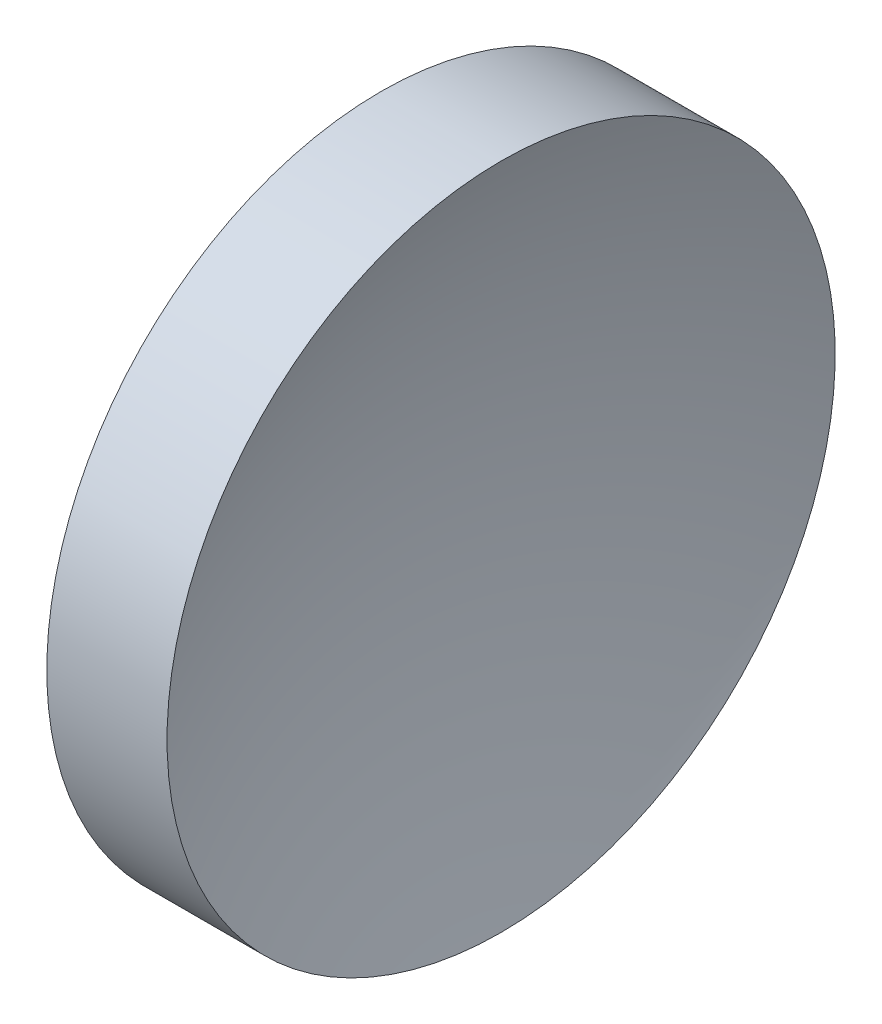
SolidWorks part; units mm, degrees
ref_plane "前视基准面" through (0, 0, 0) normal (0, 0, 1) x (1, 0, 0)
ref_plane "上视基准面" through (0, 0, 0) normal (0, 1, 0) x (1, 0, 0)
ref_plane "右视基准面" through (0, 0, 0) normal (1, 0, 0) x (0, 0, -1)
sketch "草图1" plane through (0, 0, 0) normal (0, 0, 1) x (1, 0, 0)
  line L0 (55.0074, 32.5787) -> (69.3049, 32.5787) construction
  line L1 (57.3582, 32.5787) -> (57.3582, 45.0787)
  line L2 (59.3582, 32.5787) -> (57.3582, 32.5787)
  line L3 (57.3582, 45.0787) -> (61.8582, 45.0787)
  arc A0 (61.8582, 45.0787) -> (59.3582, 32.5787) centre (91.8582, 32.5787) ccw
  dimension "D3" = 32.5
  dimension "D1" = 4.5
  dimension "D2" = 12.5
revolve "旋转1" add sketch "草图1" angle 360 about L0
